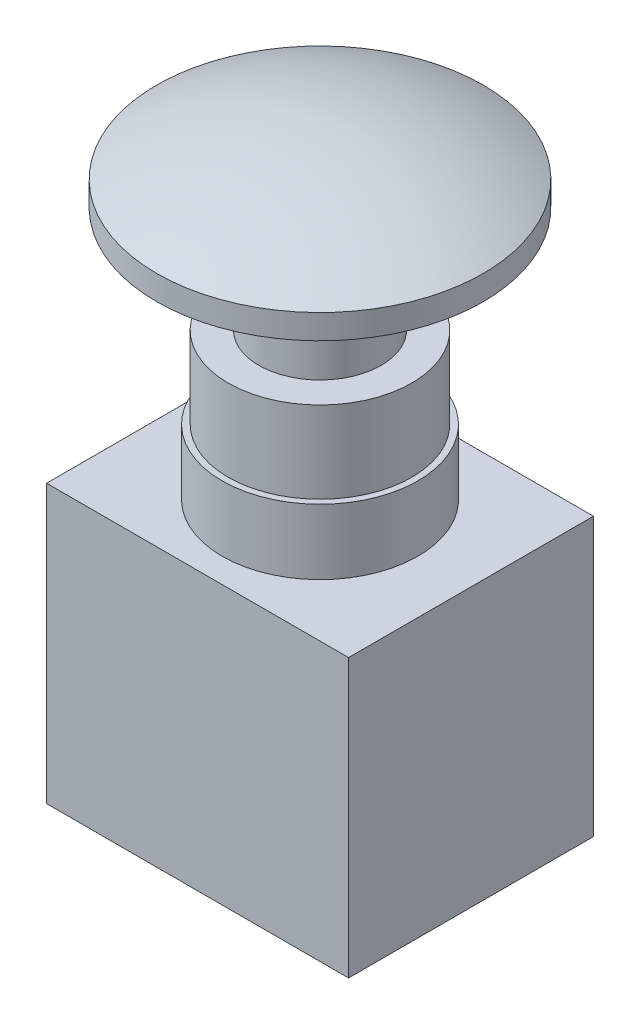
SolidWorks part; units mm, degrees
ref_plane "Спереди" through (0, 0, 0) normal (0, 0, 1) x (1, 0, 0)
ref_plane "Сверху" through (0, 0, 0) normal (0, 1, 0) x (1, 0, 0)
ref_plane "Справа" through (0, 0, 0) normal (1, 0, 0) x (0, 0, -1)
sketch "Эскиз1" plane through (0, 0, 0) normal (0, 1, 0) x (1, 0, 0)
  line L1 (-18.5, -15) -> (18.5, -15)
  line L2 (-18.5, -15) -> (-18.5, 15)
  line L3 (-18.5, 15) -> (18.5, 15)
  line L4 (18.5, -15) -> (18.5, 15)
  line L5 (-18.5, -15) -> (18.5, 15) construction
  line L6 (-18.5, 15) -> (18.5, -15) construction
  point P0 (0, 0)
  dimension "D1" = 37
  dimension "D2" = 30
extrude "Бобышка-Вытянуть1" add sketch "Эскиз1" against normal blind 34
sketch "Эскиз2" plane through (0, 0, 0) normal (0, 1, 0) x (1, 0, 0)
  circle A0 centre (0, 0) radius 12
  dimension "D1" = 24
extrude "Бобышка-Вытянуть2" add sketch "Эскиз2" along normal blind 8
sketch "Эскиз3" plane through (0, 8, 0) normal (0, 1, 0) x (1, 0, 0)
  circle A0 centre (0, 0) radius 11.25
  dimension "D1" = 22.5
extrude "Бобышка-Вытянуть3" add sketch "Эскиз3" along normal blind 10
sketch "Эскиз4" plane through (0, 0, 0) normal (1, 0, 0) x (0, 0, -1)
  line L0 (0, 18) -> (0, 39)
  line L1 (11.25, 18) -> (-11.25, 18) construction
  line L2 (0, 18) -> (7.5, 18)
  line L3 (7.5, 18) -> (7.5, 26)
  line L4 (7.5, 26) -> (11.5, 26)
  line L5 (11.5, 26) -> (11.5, 31)
  line L6 (11.5, 31) -> (20, 31)
  line L7 (20, 31) -> (20, 34)
  line L8 (0, -965.3799) -> (0, 49034.6201) construction
  line L9 (-15, -34) -> (15, -34) construction
  arc A0 (0, 39) -> (20, 34) centre (0, -3.5) cw
  dimension "D1" = 15
  dimension "D2" = 23
  dimension "D3" = 40
  dimension "D4" = 8
  dimension "D5" = 3
  dimension "D6" = 5
  dimension "D7" = 73
revolve "Повернуть1" add sketch "Эскиз4" angle 360 about L8
